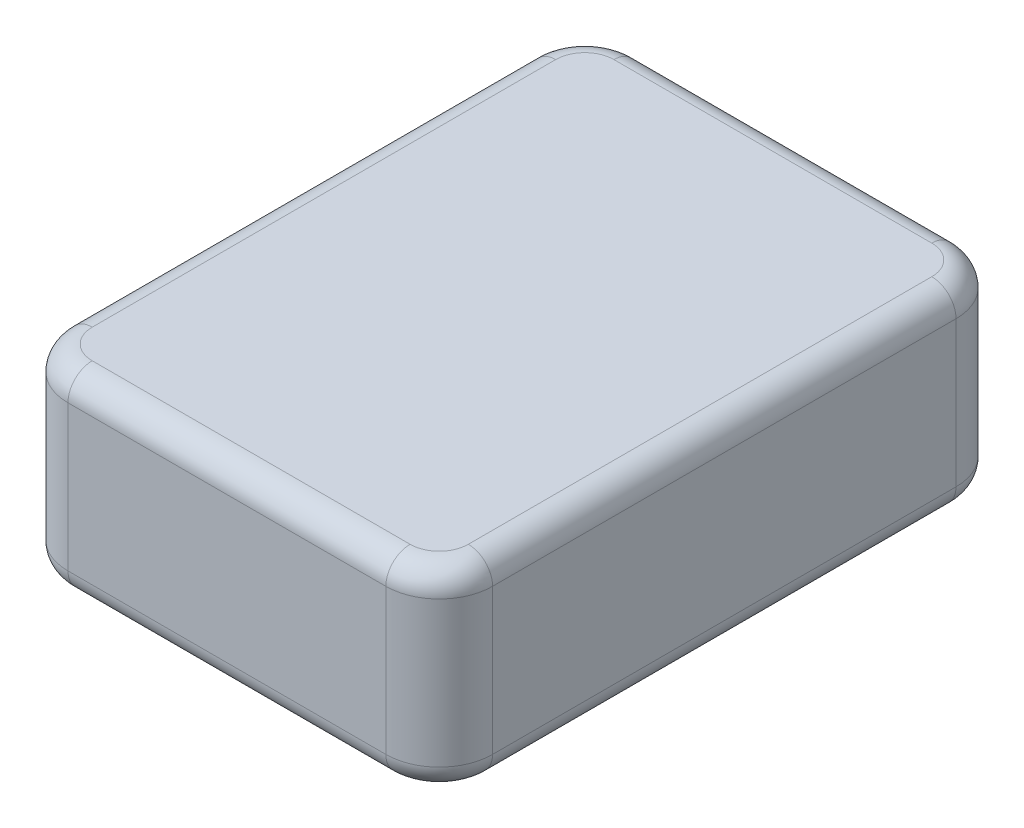
SolidWorks part; units mm, degrees
ref_plane "Front Plane" through (0, 0, 0) normal (0, 0, 1) x (1, 0, 0)
ref_plane "Top Plane" through (0, 0, 0) normal (0, 1, 0) x (1, 0, 0)
ref_plane "Right Plane" through (0, 0, 0) normal (1, 0, 0) x (0, 0, -1)
sketch "Sketch1" plane through (0, 0, 0) normal (0, 1, 0) x (1, 0, 0)
  line L1 (0, 0) -> (444.5, 0)
  line L2 (0, 0) -> (0, 596.9)
  line L3 (0, 596.9) -> (444.5, 596.9)
  line L4 (444.5, 0) -> (444.5, 596.9)
  dimension "D1" = 596.9
  dimension "D2" = 444.5
extrude "Boss-Extrude1" add sketch "Sketch1" along normal blind 203.2
fillet "Fillet1" radius 55.88 4 edges at (444.5, 101.6, -596.9) (0, 101.6, -596.9) (444.5, 101.6, 0) (0, 101.6, 0)
fillet "Fillet2" radius 25.4 16 edges at (222.25, 203.2, -596.9) (428.1331, 203.2, -580.5331) (444.5, 203.2, -298.45) (428.1331, 203.2, -16.3669) (222.25, 203.2, 0) (16.3669, 203.2, -16.3669) (0, 203.2, -298.45) (16.3669, 203.2, -580.5331) (222.25, 0, 0) (428.1331, 0, -16.3669) (444.5, 0, -298.45) (428.1331, 0, -580.5331) (222.25, 0, -596.9) (16.3669, 0, -580.5331) (0, 0, -298.45) (16.3669, 0, -16.3669)
